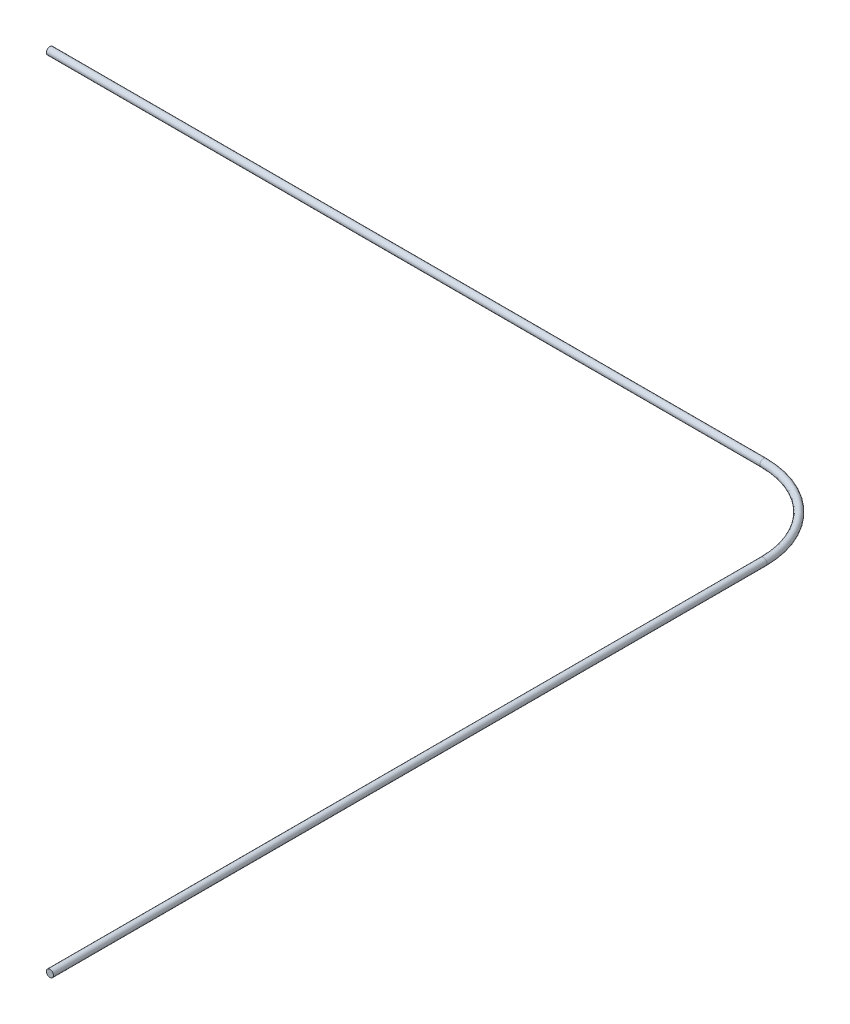
SolidWorks part; units mm, degrees
ref_plane "Front Plane" through (0, 0, 0) normal (0, 0, 1) x (1, 0, 0)
ref_plane "Top Plane" through (0, 0, 0) normal (0, 1, 0) x (1, 0, 0)
ref_plane "Right Plane" through (0, 0, 0) normal (1, 0, 0) x (0, 0, -1)
sketch "Sketch1" plane through (0, 0, 0) normal (0, 1, 0) x (1, 0, 0)
  line L0 (-50, 6) -> (0, 6)
  line L1 (6, 0) -> (6, -50)
  arc A0 (0, 6) -> (6, 0) centre (0, 0) cw
  point P5 (0, 0)
  point P7 (0, 0)
  dimension "D1" = 6
  dimension "D2" = 50
sweep "Sweep1" add path "Sketch1" circular profile diameter 0.5 parameters "D3"=0.5
